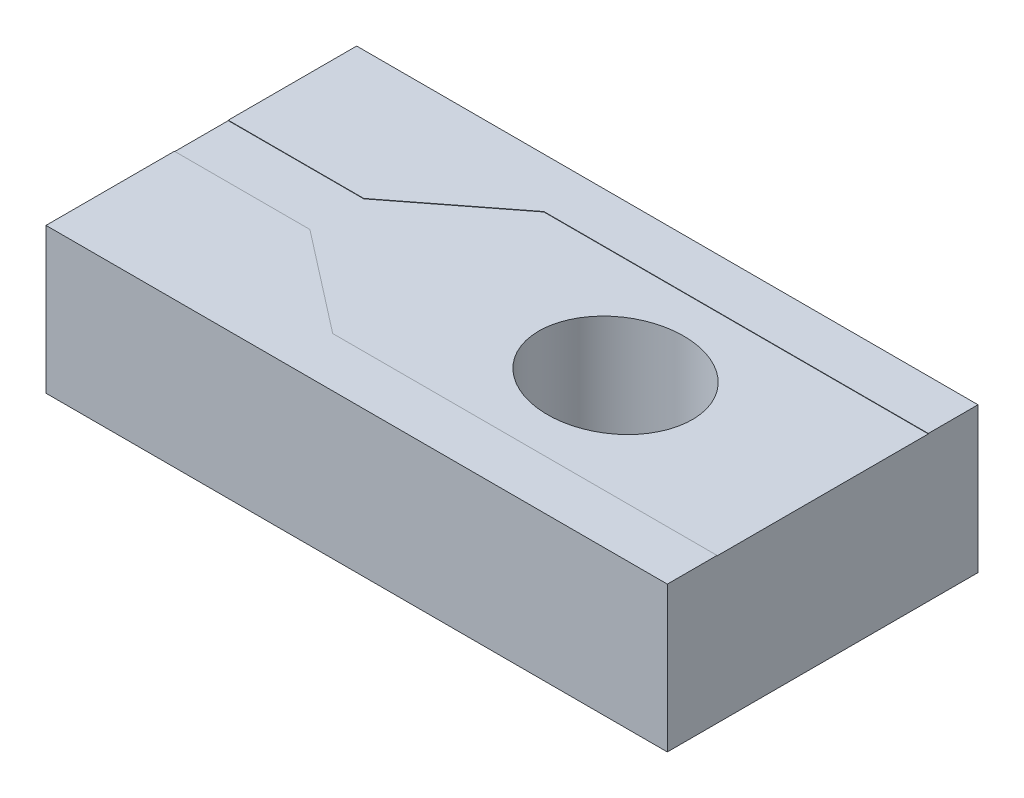
SolidWorks part; units mm, degrees
ref_plane "Front Plane" through (0, 0, 0) normal (0, 0, 1) x (1, 0, 0)
ref_plane "Top Plane" through (0, 0, 0) normal (0, 1, 0) x (1, 0, 0)
ref_plane "Right Plane" through (0, 0, 0) normal (1, 0, 0) x (0, 0, -1)
sketch "Sketch1" plane through (0, 0, 0) normal (0, 1, 0) x (1, 0, 0)
  line L0 (-37.075, 0) -> (37.075, 0) construction
  line L1 (0, 32.9) -> (0, -32.9) construction
  line L3 (100, 75) -> (-200, 75)
  line L4 (100, 75) -> (100, -75)
  line L5 (100, -75) -> (-200, -75)
  line L6 (-200, 75) -> (-200, -75)
  ellipse E0 centre (0, 0) end of major axis (-37.075, 0) minor radius 32.9
  point P15 (100, 0)
  dimension "D1" = 74.15
  dimension "D2" = 65.8
  dimension "D3" = 150
  dimension "D4" = 100
  dimension "D5" = 200
extrude "Boss-Extrude1" add sketch "Sketch1" along normal blind 70
sketch "Sketch2" plane through (0, 70, 0) normal (0, 1, 0) x (1, 0, 0)
  line L0 (100, 51) -> (-85.575, 51)
  line L1 (-85.575, 51) -> (-134.575, 13)
  line L2 (-134.575, 13) -> (-200, 13)
  line L3 (-200, -13) -> (-134.575, -13)
  line L4 (-134.575, -13) -> (-85.575, -51)
  line L5 (-85.575, -51) -> (100, -51)
  line L6 (-134.575, 13) -> (-134.575, -13) construction
  line L7 (-85.575, 51) -> (-85.575, -51) construction
  line L8 (-200, 75) -> (-200, -75) construction
  line L9 (100, 75) -> (100, -75) construction
  line L10 (100, 51) -> (100, 75)
  line L11 (100, 75) -> (-200, 75)
  line L12 (-200, 75) -> (-200, 13)
  line L13 (-200, -13) -> (-200, -75)
  line L14 (-200, -75) -> (100, -75)
  line L15 (100, -75) -> (100, -51)
  point P7 (-134.575, 0)
  point P10 (-85.575, 0)
  dimension "D1" = 26
  dimension "D2" = 102
  dimension "D3" = 97.5
  dimension "D4" = 49
extrude "Boss-Extrude2" add sketch "Sketch2" along normal blind 0.2
ref_plane "Plane1" through (-37.075, 0, 0) normal (1, 0, 0) x (0, 0, -1)
ref_plane "Plane2" through (37.075, 0, 0) normal (1, 0, 0) x (0, 0, -1)
